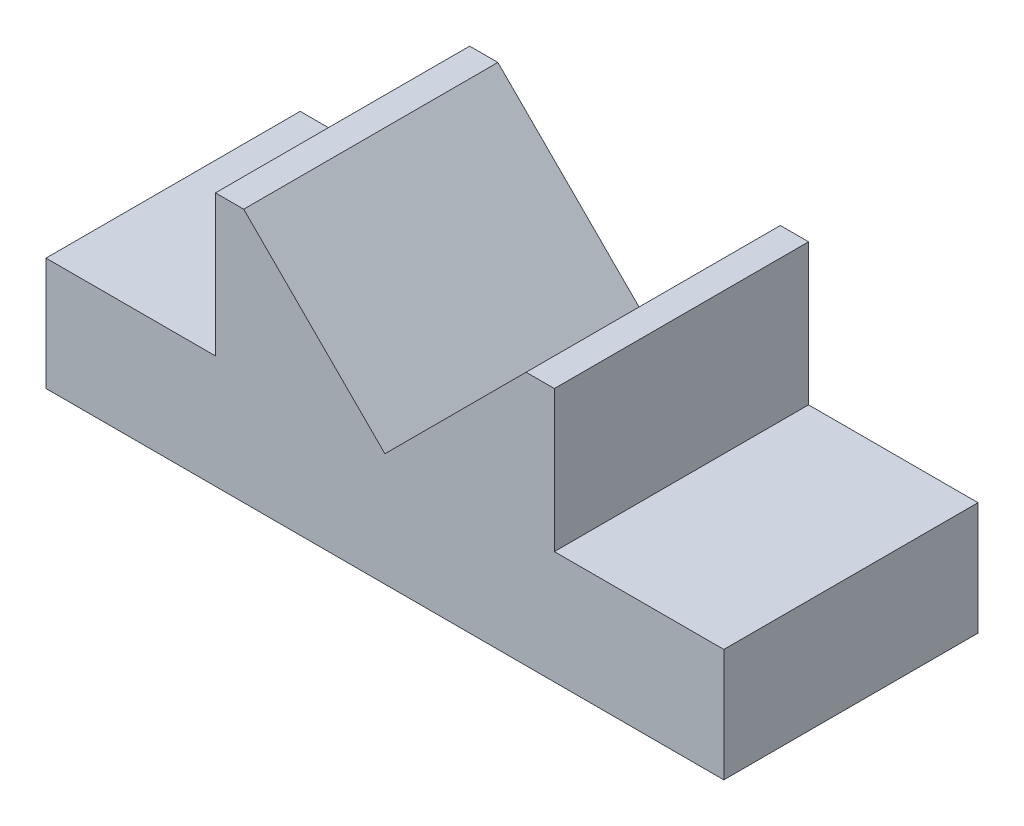
SolidWorks part; units mm, degrees
ref_plane "Front Plane" through (0, 0, 0) normal (0, 0, 1) x (1, 0, 0)
ref_plane "Top Plane" through (0, 0, 0) normal (0, 1, 0) x (1, 0, 0)
ref_plane "Right Plane" through (0, 0, 0) normal (1, 0, 0) x (0, 0, -1)
sketch "Sketch1" plane through (0, 0, 0) normal (0, 0, 1) x (1, 0, 0)
  line L0 (-601.0975, 0) -> (29453.7763, 0) construction
  line L1 (0, -601.0975) -> (0, 29453.7763) construction
  line L3 (60, 0) -> (-60, 0)
  line L4 (-60, 0) -> (-60, 20)
  line L5 (-60, 20) -> (-30, 20)
  line L6 (-30, 20) -> (-30, 45)
  line L7 (-30, 45) -> (-25, 45)
  line L8 (-25, 45) -> (0, 20)
  line L9 (601.0975, 0) -> (-29453.7763, 0) construction
  line L10 (25, 45) -> (0, 20)
  line L11 (30, 45) -> (25, 45)
  line L12 (30, 20) -> (30, 45)
  line L13 (60, 20) -> (30, 20)
  line L14 (60, 0) -> (60, 20)
  point P4 (0, 0)
  point P19 (0, 0)
  dimension "D1" = 60
  dimension "D2" = 20
  dimension "D3" = 45
  dimension "D4" = 5
  dimension "D5" = 30
  dimension "D6" = 45
  dimension "D7" = 30
extrude "Boss-Extrude1" add sketch "Sketch1" along normal blind 45
